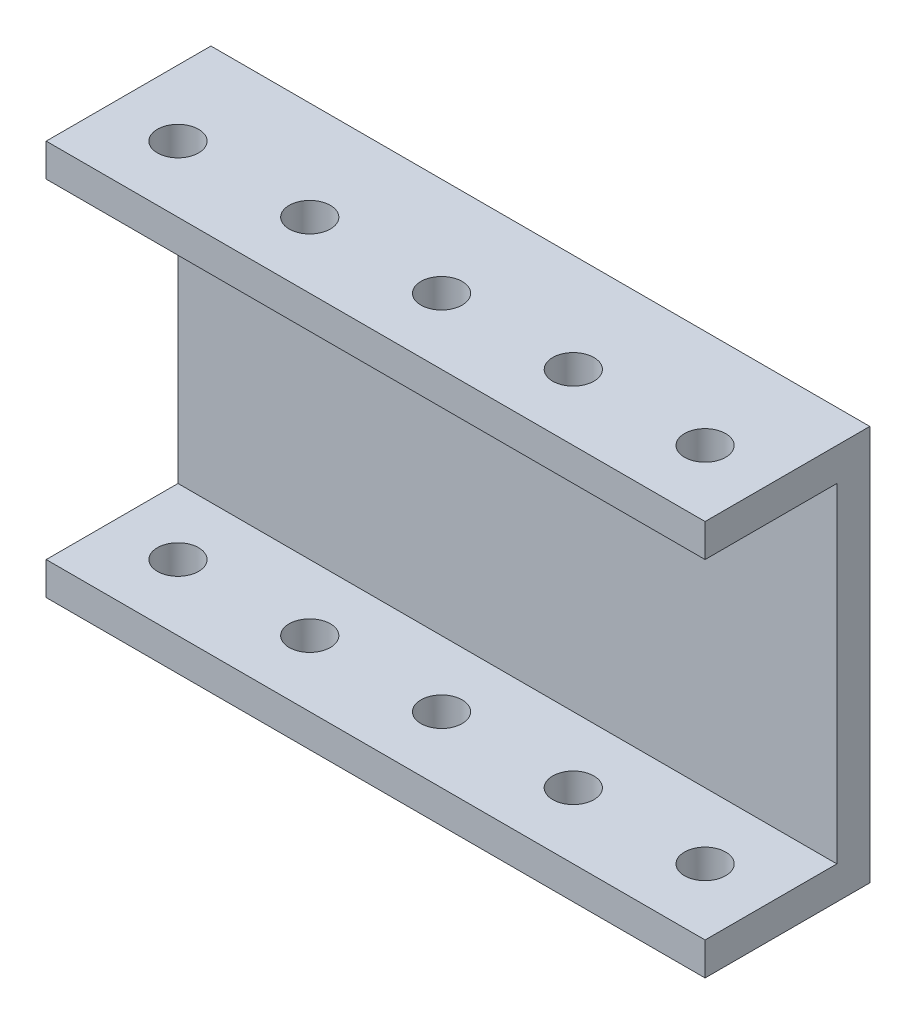
SolidWorks part; units mm, degrees
ref_plane "Front Plane" through (0, 0, 0) normal (0, 0, 1) x (1, 0, 0)
ref_plane "Top Plane" through (0, 0, 0) normal (0, 1, 0) x (1, 0, 0)
ref_plane "Right Plane" through (0, 0, 0) normal (1, 0, 0) x (0, 0, -1)
sketch "Sketch1" plane through (0, 0, 0) normal (1, 0, 0) x (0, 0, -1)
  line L1 (-2.8095, 38.7474) -> (22.5905, 38.7474)
  line L2 (-2.8095, 38.7474) -> (-2.8095, 32.3974)
  line L3 (-2.8095, 32.3974) -> (22.5905, 32.3974)
  line L4 (22.5905, 38.7474) -> (22.5905, 32.3974)
  line L5 (22.5905, 38.7474) -> (28.9405, 38.7474)
  line L6 (22.5905, 38.7474) -> (22.5905, -37.4526)
  line L7 (22.5905, -37.4526) -> (28.9405, -37.4526)
  line L8 (28.9405, 38.7474) -> (28.9405, -37.4526)
  line L9 (22.5905, -37.4526) -> (-2.8095, -37.4526)
  line L10 (22.5905, -37.4526) -> (22.5905, -31.1026)
  line L11 (22.5905, -31.1026) -> (-2.8095, -31.1026)
  line L12 (-2.8095, -37.4526) -> (-2.8095, -31.1026)
  dimension "D1" = 6.35
  dimension "D2" = 6.35
  dimension "D3" = 6.35
  dimension "D4" = 63.5
  dimension "D5" = 31.75
extrude "Boss-Extrude1" add sketch "Sketch1" along normal blind 127 contours L4 L1 L2 L3 | L8 L5 L4 L6 L7 | L12 L9 L6 L11
sketch "Sketch2" plane through (0, 38.7474, 0) normal (0, 1, 0) x (1, 0, 0)
  line L0 (0, 9.8905) -> (127, 9.8905) construction
  line L3 (12.7, 9.8905) -> (114.3, 9.8905) construction
  line L4 (0, -2.8095) -> (0, 28.9405) construction
  line L5 (127, -2.8095) -> (127, 28.9405) construction
  line L6 (127, -2.8095) -> (0, -2.8095) construction
  circle A0 centre (114.3, 9.8905) radius 3.9687
  circle A1 centre (88.9, 9.8905) radius 3.9687
  circle A2 centre (63.5, 9.8905) radius 3.9687
  circle A3 centre (38.1, 9.8905) radius 3.9687
  circle A4 centre (12.7, 9.8905) radius 3.9687
  point P9 (63.5, 9.8905)
  dimension "D1" = 7.9375
  dimension "D3" = 12.7
  dimension "D4" = 12.7
  dimension "D2" = 5
extrude "Cut-Extrude1" cut sketch "Sketch2" against normal through all
